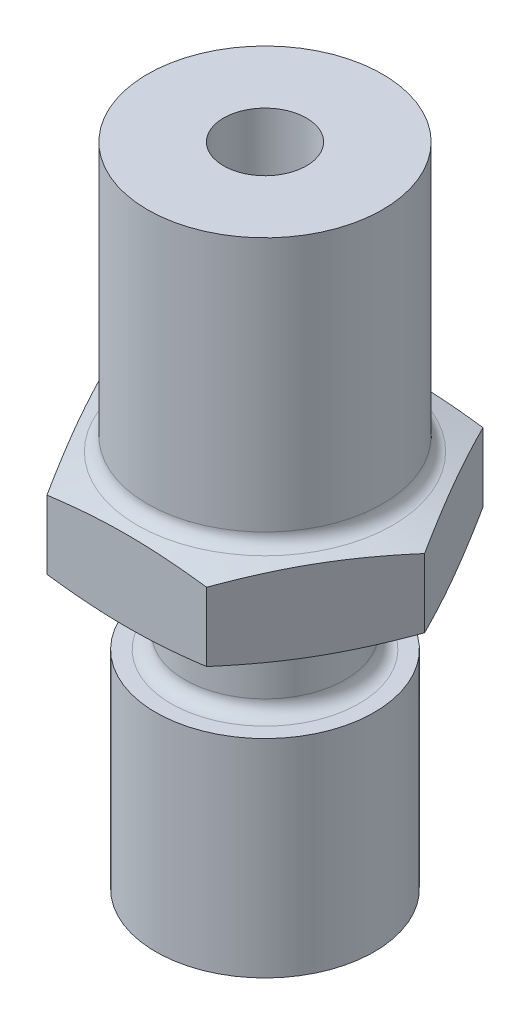
SolidWorks part; units mm, degrees
ref_plane "Front Plane" through (0, 0, 0) normal (0, 0, 1) x (1, 0, 0)
ref_plane "Top Plane" through (0, 0, 0) normal (0, 1, 0) x (1, 0, 0)
ref_plane "Right Plane" through (0, 0, 0) normal (1, 0, 0) x (0, 0, -1)
sketch "Sketch1" plane through (0, 0, 0) normal (0, 1, 0) x (1, 0, 0)
  circle A0 centre (0, 0) radius 4.25
  dimension "D1" = 8.5
extrude "Boss-Extrude1" add sketch "Sketch1" along normal blind 9.6
sketch "Sketch2" plane through (0, 0, 0) normal (0, -1, 0) x (1, 0, 0)
  line L1 (-2.8868, 5) -> (-5.7735, 0)
  line L2 (-5.7735, 0) -> (-2.8868, -5)
  line L3 (-2.8868, -5) -> (2.8868, -5)
  line L4 (2.8868, -5) -> (5.7735, 0)
  line L5 (5.7735, 0) -> (2.8868, 5)
  line L6 (2.8868, 5) -> (-2.8868, 5)
  circle A0 centre (0, 0) radius 5 construction
  dimension "D1" = 10
extrude "Boss-Extrude2" add sketch "Sketch2" along normal blind 3.3
sketch "Sketch3" plane through (0, -3.3, 0) normal (0, -1, 0) x (1, 0, 0)
  circle A2 centre (0, 0) radius 4.25
  circle A3 centre (0, 0) radius 4.25
  dimension "D1" = 0
extrude "Cut-Extrude4" cut sketch "Sketch3" against normal blind 3.3 draft 75 flip side to cut
sketch "Sketch5" plane through (0, 0, 0) normal (0, 1, 0) x (1, 0, 0)
  circle A2 centre (0, 0) radius 4.25
  circle A3 centre (0, 0) radius 4.25
  dimension "D1" = 0
extrude "Cut-Extrude5" cut sketch "Sketch5" against normal blind 3.3 draft 75 flip side to cut
sketch "Sketch6" plane through (0, -3.3, 0) normal (0, -1, 0) x (1, 0, 0)
  circle A0 centre (0, 0) radius 2.9
  dimension "D1" = 5.8
extrude "Boss-Extrude3" add sketch "Sketch6" along normal blind 3
sketch "Sketch7" plane through (0, -6.3, 0) normal (0, -1, 0) x (1, 0, 0)
  circle A0 centre (0, 0) radius 3.95
  dimension "D1" = 7.9
extrude "Boss-Extrude4" add sketch "Sketch7" along normal blind 7.5
sketch "Sketch8" plane through (0, -13.8, 0) normal (0, -1, 0) x (1, 0, 0)
  circle A0 centre (0, 0) radius 1.5
  dimension "D1" = 3
extrude "Cut-Extrude6" cut sketch "Sketch8" against normal through all
sketch "Sketch9" plane through (0, -13.8, 0) normal (0, -1, 0) x (1, 0, 0)
  circle A0 centre (0, 0) radius 2.25
  dimension "D1" = 4.5
extrude "Cut-Extrude7" cut sketch "Sketch9" against normal blind 10
fillet "Fillet1" radius 0.5 3 edges at (0, -6.3, -2.9) (0, -3.3, -2.9) (0, 0, 4.25)
sketch "Sketch10" plane through (0, 0, 0) normal (0, 0, 1) x (1, 0, 0)
  line L0 (4.25, 9.6) -> (-4.25, 9.6) construction
  circle A0 centre (0, 5.6) radius 1.5
  dimension "D1" = 3
  dimension "D2" = 4
extrude "Cut-Extrude8" cut sketch "Sketch10" against normal through all
chamfer "Chamfer1" distance 1 angle 45 1 edges at (0, -13.8, -2.25)
